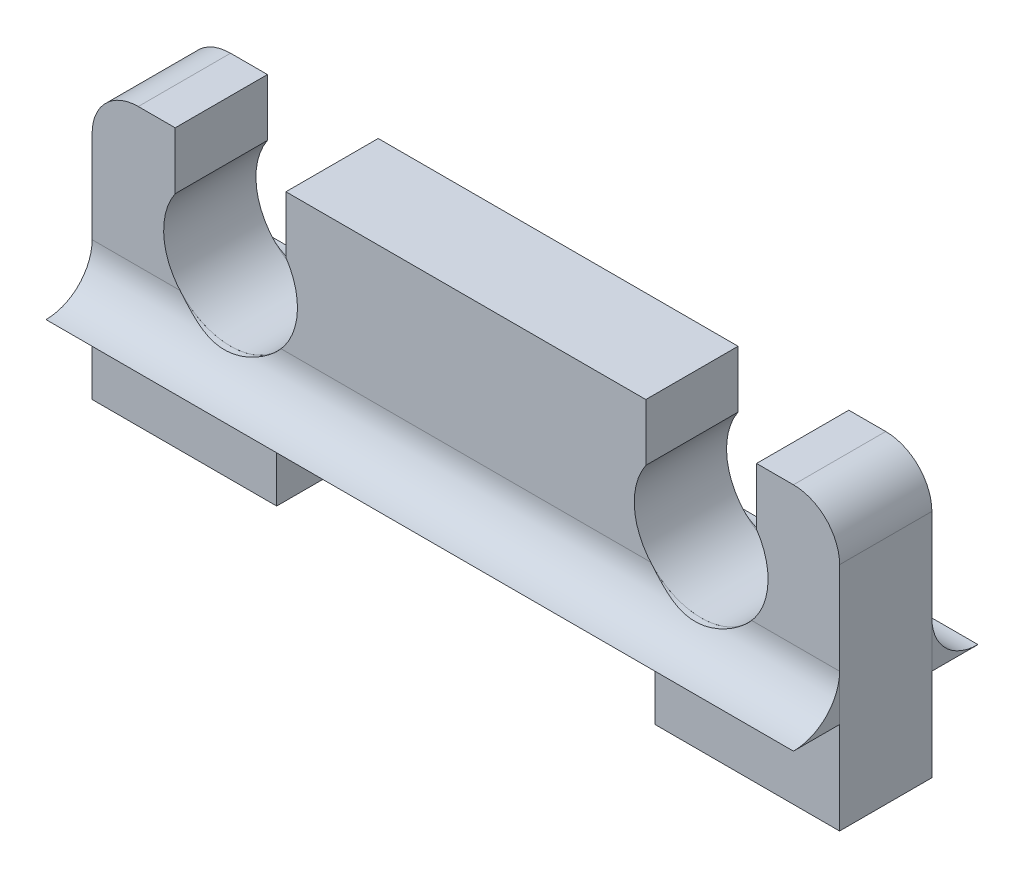
SolidWorks part; units mm, degrees
ref_plane "Front Plane" through (0, 0, 0) normal (0, 0, 1) x (1, 0, 0)
ref_plane "Top Plane" through (0, 0, 0) normal (0, 1, 0) x (1, 0, 0)
ref_plane "Right Plane" through (0, 0, 0) normal (1, 0, 0) x (0, 0, -1)
sketch "Sketch1" plane through (0, 0, 0) normal (0, 0, 1) x (1, 0, 0)
  line L0 (4, 8) -> (12.2, 8)
  line L1 (4, 4) -> (12.2, 4)
  line L2 (16.2, 0) -> (16.2, 7)
  line L3 (0, 0) -> (4, 0)
  line L4 (4, 0) -> (4, 4)
  line L5 (2, 7) -> (2, 8)
  line L6 (12.2, 8) -> (12.2, 7)
  line L7 (1, 8) -> (2, 8)
  line L8 (4, 8) -> (4, 7)
  line L9 (14.2, 8) -> (15.2, 8)
  line L10 (14.2, 8) -> (14.2, 7)
  line L11 (12.2, 0) -> (12.2, 4)
  line L12 (0, 0) -> (0, 7)
  line L13 (16.2, 0) -> (12.2, 0)
  line L14 (8.1, 4) -> (8.1, 8) construction
  arc A0 (15.2, 8) -> (16.2, 7) centre (15.2, 7) cw
  arc A1 (2, 7) -> (4, 7) centre (3, 5.95) ccw
  arc A2 (14.2, 7) -> (12.2, 7) centre (13.2, 5.95) cw
  arc A3 (1, 8) -> (0, 7) centre (1, 7) ccw
  dimension "D1" = 1.45
  dimension "D2" = 1
  dimension "D3" = 3
  dimension "D4" = 4
  dimension "D5" = 8.1
  dimension "D6" = 1
  dimension "D7" = 1
  dimension "D8" = 1
extrude "Boss-Extrude1" add sketch "Sketch1" along normal blind 2
sketch "Sketch2" plane through (0, 0, 0) normal (-1, 0, 0) x (0, 0, 1)
  line L0 (1, 0) -> (1, 7) construction
  line L1 (2, 7) -> (2, 0) construction
  line L2 (2, 4) -> (2, 5)
  line L3 (2, 4) -> (3, 4)
  line L4 (2, 0) -> (0, 0) construction
  line L5 (2, 7) -> (0, 7) construction
  line L6 (0, 4) -> (-1, 4)
  line L7 (0, 4) -> (0, 5)
  arc A0 (2, 5) -> (3, 4) centre (3, 5) ccw
  arc A1 (0, 5) -> (-1, 4) centre (-1, 5) cw
  dimension "D2" = 1
  dimension "D1" = 4
extrude "Boss-Extrude2" add sketch "Sketch2" against normal blind 16.2 separate body
sketch "Sketch3" plane through (0, 0, 2) normal (0, 0, 1) x (1, 0, 0)
  line L0 (0, 0) -> (0, 2)
  line L1 (0, 7) -> (0, 0) construction
  line L2 (0, 2) -> (4, 2)
  line L3 (4, 0) -> (4, 4) construction
  line L4 (4, 2) -> (4, 0)
  line L5 (4, 0) -> (0, 0)
  line L6 (8.1, 8) -> (8.1, 0) construction
  line L7 (12.2, 8) -> (4, 8) construction
  line L8 (12.2, 0) -> (16.2, 0)
  line L9 (12.2, 2) -> (12.2, 0)
  line L10 (16.2, 2) -> (12.2, 2)
  line L11 (16.2, 0) -> (16.2, 2)
extrude "Cut-Extrude1" cut sketch "Sketch3" against normal through all
sketch "Sketch5" plane through (0, 8, 0) normal (0, 1, 0) x (1, 0, 0)
  line L0 (1.8, 0) -> (4.2, 0)
  line L1 (4.45, 0) -> (1.55, 0) construction
  line L2 (12.2, 0) -> (4, 0) construction
  line L3 (3, 0) -> (3, -3) construction
  line L4 (16.2, -3) -> (0, -3) construction
  line L5 (4.2, 0) -> (4.2, -2)
  line L6 (12.2, -2) -> (4, -2) construction
  line L7 (4.2, -2) -> (1.8, -2)
  line L8 (1.8, 0) -> (1.8, -2)
  line L9 (8.1, 0) -> (8.1, -3) construction
  line L10 (14.4, 0) -> (14.4, -2)
  line L11 (12, -2) -> (14.4, -2)
  line L12 (12, 0) -> (12, -2)
  line L13 (14.4, 0) -> (12, 0)
  point P14 (3, -2)
  point P21 (13.2, -2)
  dimension "D1" = 1.2
extrude "Cut-Extrude4" cut sketch "Sketch5" against normal up to body
ref_plane "Plane1" through (0, 0, 1) normal (0, 0, 1) x (1, 0, 0)
sketch "Sketch8" plane through (0, 0, 1) normal (0, 0, 1) x (1, 0, 0)
  line L0 (8.1, 8) -> (8.1, 10.621) construction
  line L1 (12, 8) -> (4.2, 8) construction
  circle A0 centre (3, 5.95) radius 1.45
  circle A1 centre (13.2, 5.95) radius 1.45
  dimension "D1" = 2.9
extrude "Cut-Extrude6" cut sketch "Sketch8" against normal through all both and the other way through all
equation "\"D5@Sketch1\"= \"fingerWidth@parametersSketch@prostheticParameters.SLDPRT\" / 2"
equation "\"D1@Boss-Extrude2\"= \"fingerWidth@parametersSketch@prostheticParameters.SLDPRT\"'Radius of Tube Driver"
equation "\"D1@Sketch1\"= 1.25 + \"tol1@parametersSketch@prostheticParameters.SLDPRT\" / 2"
equation "\"D1@Sketch5\"= 1 + \"tol2@parametersSketch@prostheticParameters.SLDPRT\" / 2"
equation "\"D1@Sketch8\"= 2.5 + \"tol1@parametersSketch@prostheticParameters.SLDPRT\""
